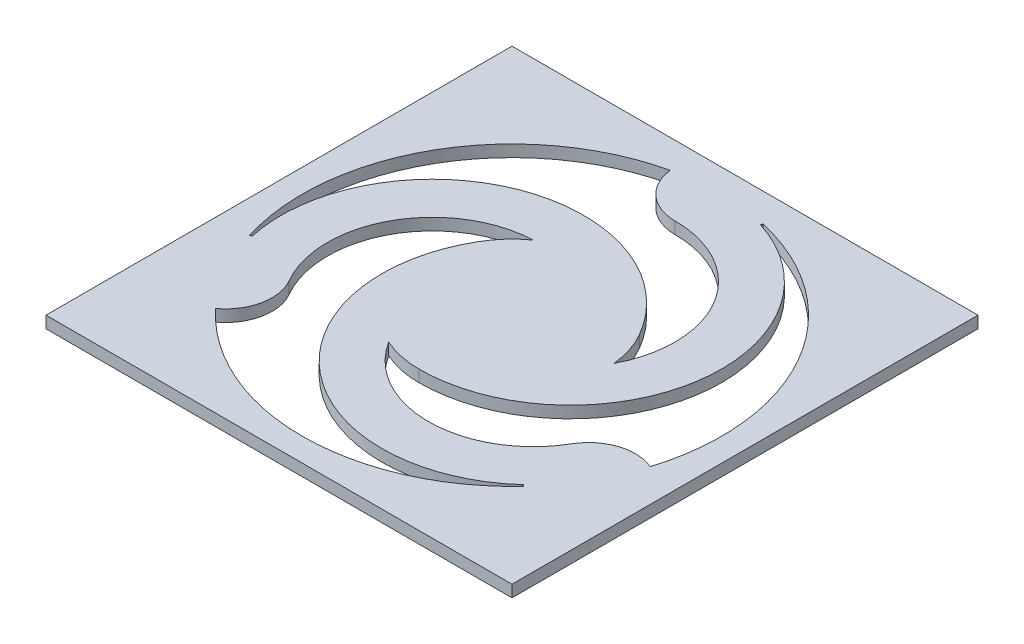
SolidWorks part; units mm, degrees
ref_plane "Front Plane" through (0, 0, 0) normal (0, 0, 1) x (1, 0, 0)
ref_plane "Top Plane" through (0, 0, 0) normal (0, 1, 0) x (1, 0, 0)
ref_plane "Right Plane" through (0, 0, 0) normal (1, 0, 0) x (0, 0, -1)
sketch "Sketch1" plane through (0, 0, 0) normal (0, 1, 0) x (1, 0, 0)
  line L1 (0, 0) -> (5, 0)
  line L2 (0, 0) -> (0, 5)
  line L3 (0, 5) -> (5, 5)
  line L4 (5, 0) -> (5, 5)
  line L6 (2.5, 4.75) -> (2.5, 1.5) construction
  circle A0 centre (2.5, 2.5) radius 1
  circle A1 centre (2.5, 2.5) radius 2.25
  arc A2 (2.5, 1.5) -> (2.994, 4.6731) centre (2.5, 3.125) ccw
  arc A5 (2.994, 4.6731) -> (2.9969, 4.6944) centre (2.5, 4.75) ccw
  arc A6 (2.0031, 4.6944) -> (2.5, 4.25) centre (2.5, 4.75) ccw
  arc A7 (3.495, 2.6) -> (2.5, 4.25) centre (2.5, 3.125) ccw
  arc A8 (2.994, 4.6731) -> (2.9969, 4.6944) centre (2.5, 4.75) ccw
  arc A9 (4.1349, 0.9856) -> (4.152, 0.9724) centre (4.4486, 1.375) ccw
  arc A10 (4.6489, 1.8331) -> (4.0155, 1.625) centre (4.4486, 1.375) ccw
  arc A11 (2.0891, 1.5883) -> (4.0155, 1.625) centre (3.0413, 2.1875) ccw
  arc A12 (1.634, 3) -> (4.1349, 0.9856) centre (3.0413, 2.1875) ccw
  arc A13 (0.371, 1.8413) -> (0.3511, 1.8331) centre (0.5514, 1.375) ccw
  arc A14 (0.848, 0.9724) -> (0.9845, 1.625) centre (0.5514, 1.375) ccw
  arc A15 (1.9159, 3.3117) -> (0.9845, 1.625) centre (1.9587, 2.1875) ccw
  arc A16 (3.366, 3) -> (0.371, 1.8413) centre (1.9587, 2.1875) ccw
  point P8 (2.5, 5)
  point P9 (5, 2.5)
  point P36 (2.5, 2.5)
  dimension "D3" = 2
  dimension "D4" = 4.5
  dimension "D5" = 0.5
  dimension "D1" = 5
  dimension "D2" = 5
  dimension "D6" = 3
extrude "Boss-Extrude1" add sketch "Sketch1" along normal blind 0.127 contours L6 A16 A13 A1 A14 A15 A0 | A16 L6 A0 | A0 A12 A9 A1 A10 A11 | A1 L6 A7 A0 A2 A5 | L6 A1 A6 | A0 L6 | L6 A0 | L1 L4 L3 L2 A1
